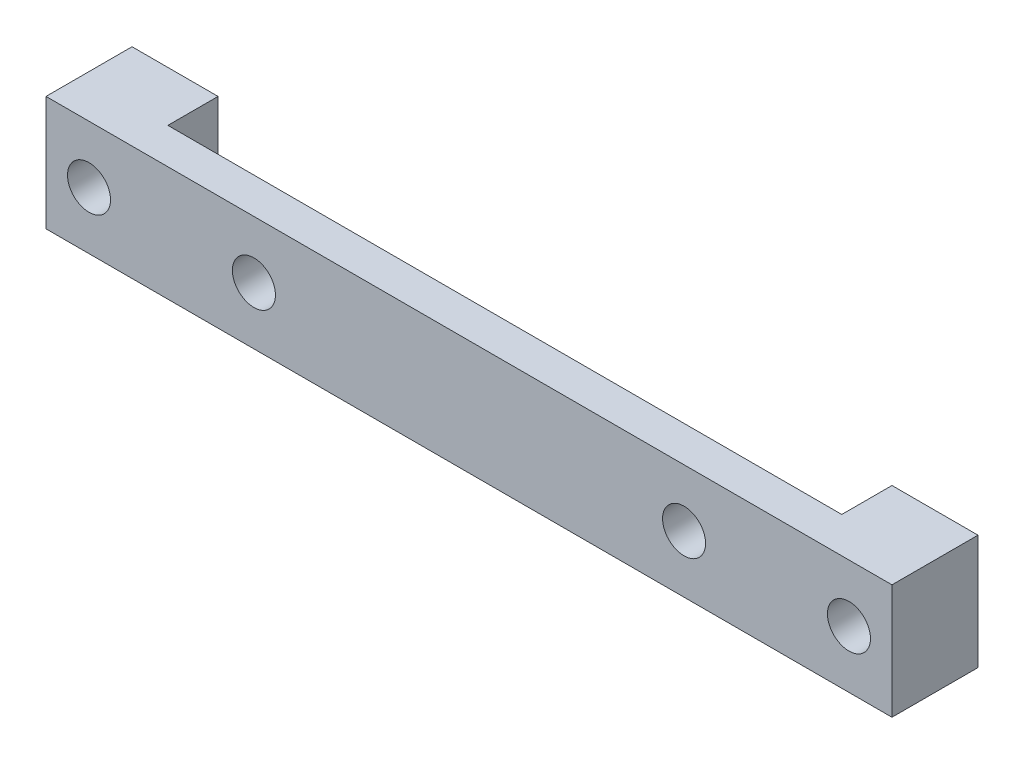
SolidWorks part; units mm, degrees
ref_plane "Front Plane" through (0, 0, 0) normal (0, 0, 1) x (1, 0, 0)
ref_plane "Top Plane" through (0, 0, 0) normal (0, 1, 0) x (1, 0, 0)
ref_plane "Right Plane" through (0, 0, 0) normal (1, 0, 0) x (0, 0, -1)
sketch "Sketch1" plane through (0, 0, 0) normal (0, 0, 1) x (1, 0, 0)
  line L1 (-29.5, 4) -> (29.5, 4)
  line L2 (-29.5, 4) -> (-29.5, -4)
  line L3 (-29.5, -4) -> (29.5, -4)
  line L4 (29.5, 4) -> (29.5, -4)
  line L5 (-29.5, 4) -> (29.5, -4) construction
  line L6 (-29.5, -4) -> (29.5, 4) construction
  circle A0 centre (-26.5, 0) radius 1.5
  circle A1 centre (-15, 0) radius 1.5
  circle A2 centre (15, 0) radius 1.5
  circle A3 centre (26.5, 0) radius 1.5
  point P0 (0, 0)
extrude "Boss-Extrude1" add sketch "Sketch1" along normal blind 6
sketch "Sketch2" plane through (0, 4, 0) normal (0, 1, 0) x (-1, 0, 0)
  line L1 (23.5, 3.5) -> (-23.5, 3.5)
  line L2 (23.5, 3.5) -> (23.5, -3.5)
  line L3 (23.5, -3.5) -> (-23.5, -3.5)
  line L4 (-23.5, 3.5) -> (-23.5, -3.5)
  line L5 (23.5, 3.5) -> (-23.5, -3.5) construction
  line L6 (23.5, -3.5) -> (-23.5, 3.5) construction
  point P0 (0, 0)
extrude "Cut-Extrude1" cut sketch "Sketch2" against normal blind 15
